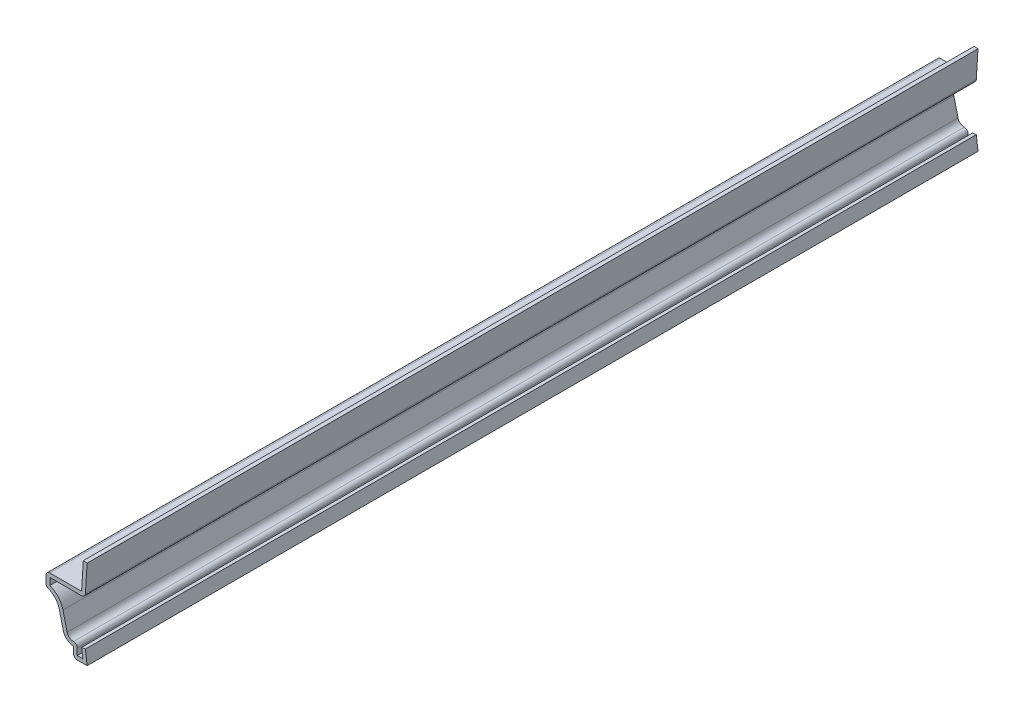
SolidWorks part; units mm, degrees
ref_plane "Front Plane" through (0, 0, 0) normal (0, 0, 1) x (1, 0, 0)
ref_plane "Top Plane" through (0, 0, 0) normal (0, 1, 0) x (1, 0, 0)
ref_plane "Right Plane" through (0, 0, 0) normal (1, 0, 0) x (0, 0, -1)
sketch "Sketch1" plane through (0, 0, 0) normal (0, 0, 1) x (1, 0, 0)
  line L0 (0, 0) -> (0, 22.4275) construction
  line L1 (-0.8873, 20.6375) -> (-1.2841, 14.2875)
  line L2 (-1.2841, 14.2875) -> (-9.525, 14.2875)
  line L3 (-9.525, 14.2875) -> (-9.525, 11.1125)
  line L4 (-6.4647, 8.171) -> (-5.4875, 4.1943)
  line L5 (-3.175, 2.3813) -> (-3.175, 0)
  line L6 (-3.175, 0) -> (0, 0)
  line L7 (0, 0) -> (-0.3969, 3.1501)
  line L8 (-0.3969, 3.1501) -> (1.7708, 3.4232) construction
  line L9 (-0.8873, 20.6375) -> (0, 20.582) construction
  arc A0 (-9.525, 11.1125) -> (-6.4647, 8.171) centre (-10.3187, 7.2239) cw
  arc A1 (-5.4875, 4.1943) -> (-3.175, 2.3813) centre (-3.175, 4.7625) ccw
  dimension "D5" = 3.9688
  dimension "D7" = 3.175
  dimension "D9" = 2.3813
  dimension "D1" = 14.2875
  dimension "D2" = 6.35
  dimension "D3" = 3.175
  dimension "D4" = 2.3813
  dimension "D6" = 0.7937
  dimension "D8" = 9.525
  dimension "D10" = 3.175
  dimension "D11" = 0.3969
  dimension "D12" = 0.889
  dimension "D13" = 0.3969
extrude "Extrude-Thin1" add sketch "Sketch1" against normal blind 206.375 thin thin type one direction reverse wall 0.889
fillet "Fillet1" radius 0.889 5 edges at (-3.175, 0, -103.1875) (-2.286, 3.564, -103.1875) (-9.525, 11.1125, -103.1875) (-9.525, 14.2875, -103.1875) (-0.449, 13.3985, -103.1875)
